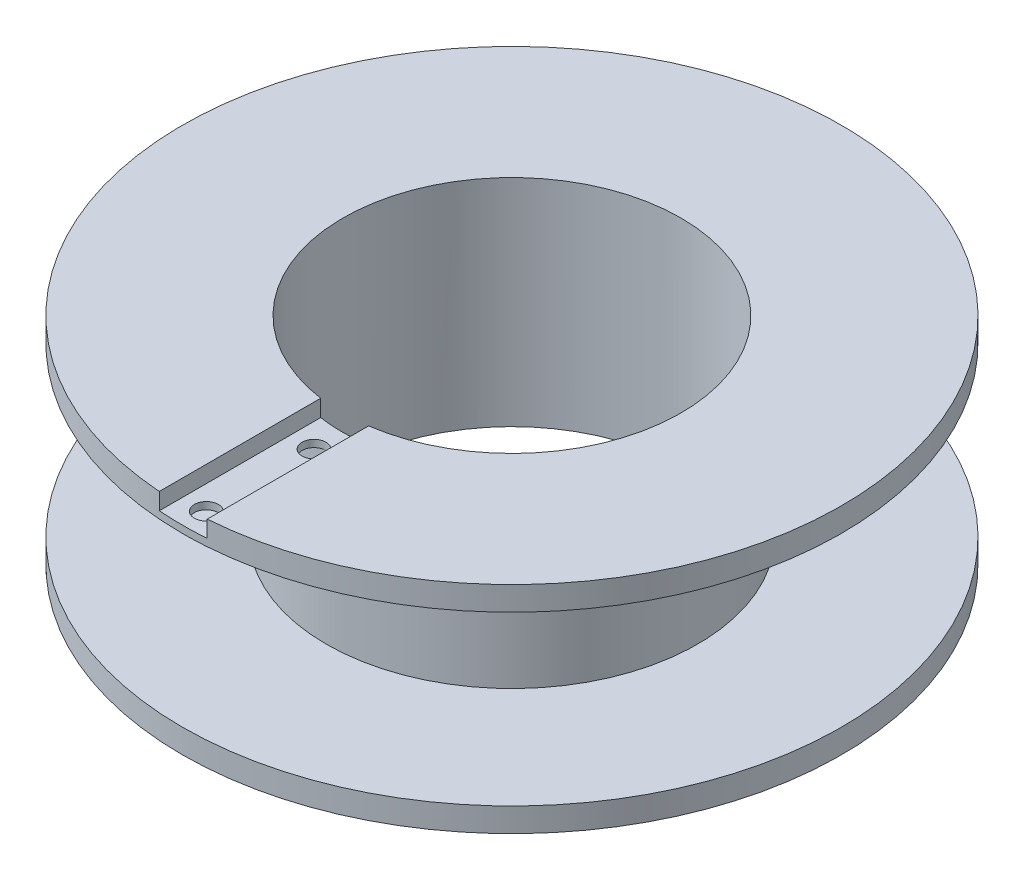
SolidWorks part; units mm, degrees
ref_plane "Plan de face" through (0, 0, 0) normal (0, 0, 1) x (1, 0, 0)
ref_plane "Plan de dessus" through (0, 0, 0) normal (0, 1, 0) x (1, 0, 0)
ref_plane "Plan de droite" through (0, 0, 0) normal (1, 0, 0) x (0, 0, -1)
sketch "Esquisse1" plane through (0, 0, 0) normal (0, 1, 0) x (1, 0, 0)
  circle A0 centre (0, 0) radius 13.75
extrude "Boss.-Extru.1" add sketch "Esquisse1" along normal blind 9
sketch "Esquisse2" plane through (0, 9, 0) normal (0, 1, 0) x (-1, 0, 0)
  circle A0 centre (0, 0) radius 7.75
extrude "Enlèv. mat.-Extru.1" cut sketch "Esquisse2" against normal blind 7 from offset 1 flip side to cut offset against normal yes
sketch "Esquisse3" plane through (0, 9, 0) normal (0, 1, 0) x (-1, 0, 0)
  circle A0 centre (0, 0) radius 7.05
extrude "Enlèv. mat.-Extru.2" cut sketch "Esquisse3" against normal up to next
sketch "Esquisse4" plane through (0, 9, 0) normal (0, 1, 0) x (-1, 0, 0)
  line L0 (0, 0) -> (0, 15.5126) construction
  line L1 (0, 7.7563) -> (3.1206, 7.7563) construction
  line L2 (0, 8.2563) -> (3.1206, 8.2563) construction
  line L3 (0, 13.75) -> (5.7541, 13.75) construction
  line L4 (0, 12.75) -> (5.7541, 12.75) construction
  circle A0 centre (0, 0) radius 13.75 construction
  circle A1 centre (0, 8.2563) radius 0.5
  circle A2 centre (0, 12.75) radius 0.5
  dimension "D1" = 0.5
  dimension "D2" = 1
extrude "Enlèv. mat.-Extru.3" cut sketch "Esquisse4" against normal up to next
sketch "Esquisse5" plane through (0, 9, 0) normal (0, 1, 0) x (-1, 0, 0)
  line L0 (0, 0) -> (0, 15.5847) construction
  line L1 (1, 0) -> (1, 15.5847)
  line L2 (-1, 0) -> (-1, 15.5847)
  line L3 (1, 15.5847) -> (-1, 15.5847)
  line L4 (-1, 0) -> (-1, 15.5847) construction
  line L5 (1, 0) -> (-1, 0)
  dimension "D1" = 1
  dimension "D2" = 1
extrude "Enlèv. mat.-Extru.4" cut sketch "Esquisse5" against normal blind 0.7
